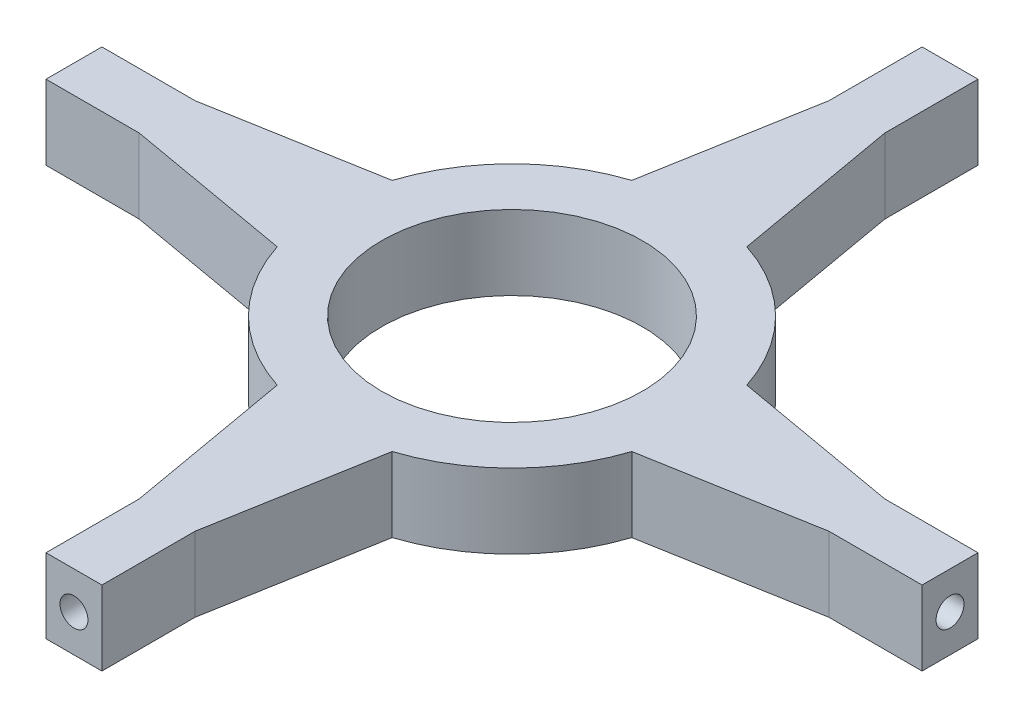
SolidWorks part; units mm, degrees
material "Chrome Stainless Steel"
ref_plane "Front Plane" through (0, 0, 0) normal (0, 0, 1) x (1, 0, 0)
ref_plane "Top Plane" through (0, 0, 0) normal (0, 1, 0) x (1, 0, 0)
ref_plane "Right Plane" through (0, 0, 0) normal (1, 0, 0) x (0, 0, -1)
sketch "Sketch1" plane through (0, 0, 0) normal (0, 1, 0) x (1, 0, 0)
  line L0 (95.1232, 30.8477) -> (185, 15)
  line L1 (185, 15) -> (235, 15)
  line L2 (235, 15) -> (235, -15)
  line L3 (235, -15) -> (185, -15)
  line L4 (185, -15) -> (95.1232, -30.8477)
  line L5 (-15, -185) -> (-30.8477, -95.1232)
  line L6 (30.8477, -95.1232) -> (15, -185)
  line L7 (15, -185) -> (15, -235)
  line L8 (-15, -235) -> (-15, -185)
  line L9 (15, -235) -> (-15, -235)
  line L10 (-185, 15) -> (-95.1232, 30.8477)
  line L11 (-95.1232, -30.8477) -> (-185, -15)
  line L12 (-185, -15) -> (-235, -15)
  line L13 (-235, 15) -> (-185, 15)
  line L14 (-235, -15) -> (-235, 15)
  line L15 (15, 185) -> (30.8477, 95.1232)
  line L16 (-30.8477, 95.1232) -> (-15, 185)
  line L17 (-15, 185) -> (-15, 235)
  line L18 (15, 235) -> (15, 185)
  line L19 (-15, 235) -> (15, 235)
  circle A0 centre (0, 0) radius 70
  arc A1 (95.1232, 30.8477) -> (30.8477, 95.1232) centre (0, 0) ccw
  arc A2 (95.1232, 30.8477) -> (30.8477, 95.1232) centre (0, 0) ccw
  arc A3 (95.1232, 30.8477) -> (30.8477, 95.1232) centre (0, 0) ccw
  arc A4 (95.1232, 30.8477) -> (30.8477, 95.1232) centre (0, 0) ccw
  arc A5 (30.8477, -95.1232) -> (95.1232, -30.8477) centre (0, 0) ccw
  arc A6 (30.8477, -95.1232) -> (95.1232, -30.8477) centre (0, 0) ccw
  arc A7 (30.8477, -95.1232) -> (95.1232, -30.8477) centre (0, 0) ccw
  arc A8 (30.8477, -95.1232) -> (95.1232, -30.8477) centre (0, 0) ccw
  arc A9 (-95.1232, -30.8477) -> (-30.8477, -95.1232) centre (0, 0) ccw
  arc A10 (-95.1232, -30.8477) -> (-30.8477, -95.1232) centre (0, 0) ccw
  arc A11 (-95.1232, -30.8477) -> (-30.8477, -95.1232) centre (0, 0) ccw
  arc A12 (-95.1232, -30.8477) -> (-30.8477, -95.1232) centre (0, 0) ccw
  arc A13 (-30.8477, 95.1232) -> (-95.1232, 30.8477) centre (0, 0) ccw
  arc A14 (-30.8477, 95.1232) -> (-95.1232, 30.8477) centre (0, 0) ccw
  arc A15 (-30.8477, 95.1232) -> (-95.1232, 30.8477) centre (0, 0) ccw
  arc A16 (-30.8477, 95.1232) -> (-95.1232, 30.8477) centre (0, 0) ccw
  point P6 (235, 0)
  point P35 (0, 0)
  dimension "D1" = 140
  dimension "D2" = 200
  dimension "D3" = 235
  dimension "D4" = 170
  dimension "D5" = 170
  dimension "D6" = 30
  dimension "D7" = 50
  dimension "D8" = 50
  dimension "D9" = 4
extrude "Boss-Extrude1" add sketch "Sketch1" along normal blind 40
sketch "Sketch2" plane through (0, 0, 235) normal (0, 0, 1) x (1, 0, 0)
  circle A0 centre (0, 20) radius 7.5
  dimension "D1" = 15
  dimension "D2" = 20
extrude "Cut-Extrude1" cut sketch "Sketch2" against normal blind 30
pattern_circular "CirPattern1" count 4 over 360 about axis through (0, 0, 0) along (0, 1, 0) of "Cut-Extrude1"
